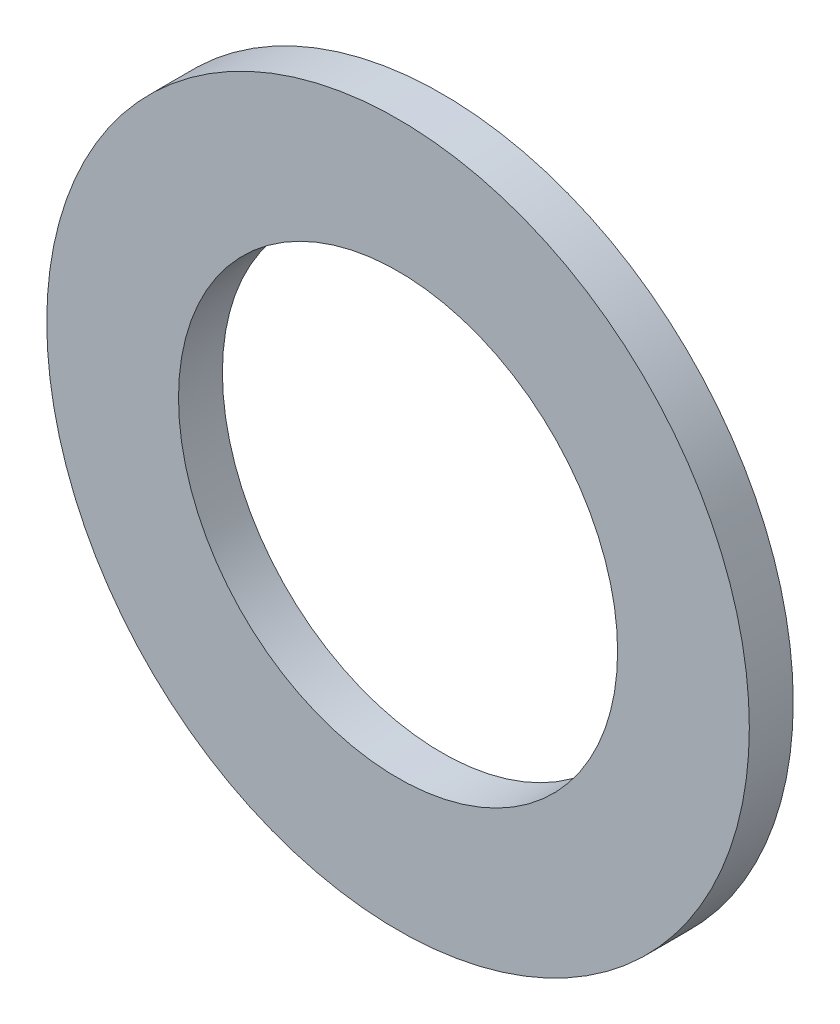
SolidWorks part; units mm, degrees
ref_plane "Front Plane" through (0, 0, 0) normal (0, 0, 1) x (1, 0, 0)
ref_plane "Top Plane" through (0, 0, 0) normal (0, 1, 0) x (1, 0, 0)
ref_plane "Right Plane" through (0, 0, 0) normal (1, 0, 0) x (0, 0, -1)
sketch "Sketch1" plane through (0, 0, 0) normal (0, 0, 1) x (1, 0, 0)
  line L0 (5, 0) -> (8, 0) construction
  circle A0 centre (0, 0) radius 5
  circle A1 centre (0, 0) radius 8
  dimension "D1" = 10
  dimension "D2" = 3
extrude "Boss-Extrude1" add sketch "Sketch1" along normal blind 1
